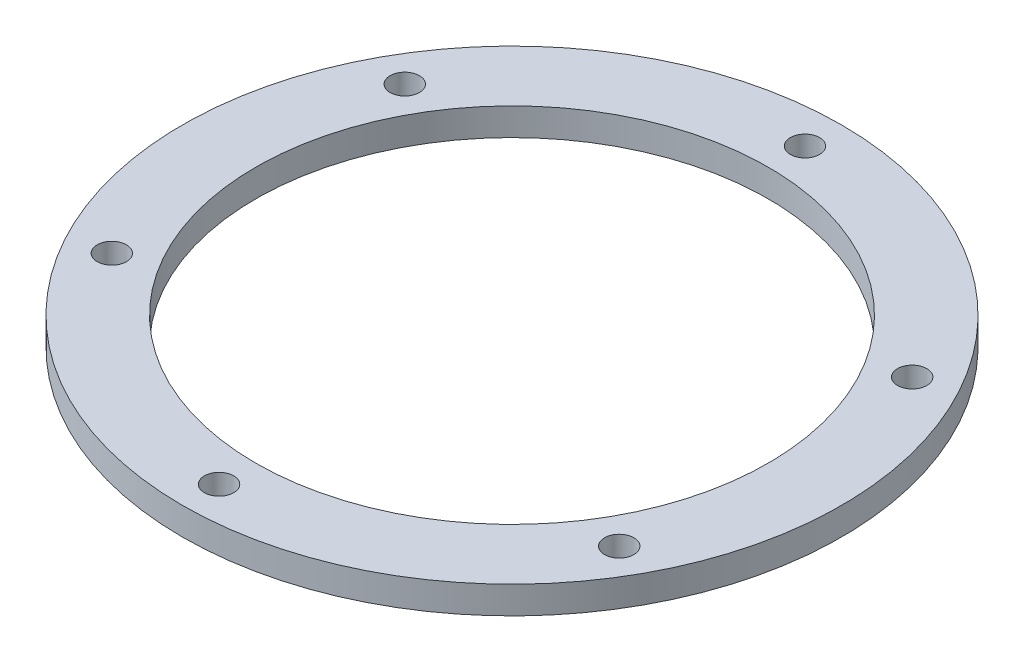
SolidWorks part; units mm, degrees
material "PET"
ref_plane "Спереди" through (0, 0, 0) normal (0, 0, 1) x (1, 0, 0)
ref_plane "Сверху" through (0, 0, 0) normal (0, 1, 0) x (1, 0, 0)
ref_plane "Справа" through (0, 0, 0) normal (1, 0, 0) x (0, 0, -1)
sketch "Эскиз1" plane through (0, 0, 0) normal (0, 1, 0) x (1, 0, 0)
  line L1 (0, -32) -> (27.7128, -16) construction
  line L2 (27.7128, -16) -> (27.7128, 16) construction
  line L3 (27.7128, 16) -> (0, 32) construction
  line L4 (0, 32) -> (-27.7128, 16) construction
  line L5 (-27.7128, 16) -> (-27.7128, -16) construction
  line L6 (-27.7128, -16) -> (0, -32) construction
  circle A0 centre (0, 0) radius 32 construction
  circle A1 centre (0, 0) radius 27.7128 construction
  circle A2 centre (0, -32) radius 1.6
  circle A3 centre (-27.7128, -16) radius 1.6
  circle A4 centre (-27.7128, 16) radius 1.6
  circle A5 centre (0, 32) radius 1.6
  circle A6 centre (27.7128, 16) radius 1.6
  circle A7 centre (27.7128, -16) radius 1.6
  circle A8 centre (0, 0) radius 36
  circle A9 centre (0, 0) radius 28
  point P23 (0, 0)
  dimension "D1" = 64
  dimension "D2" = 3.2
  dimension "D4" = 72
  dimension "D5" = 56
  dimension "D3" = 6
extrude "Бобышка-Вытянуть1" add sketch "Эскиз1" along normal blind 3
